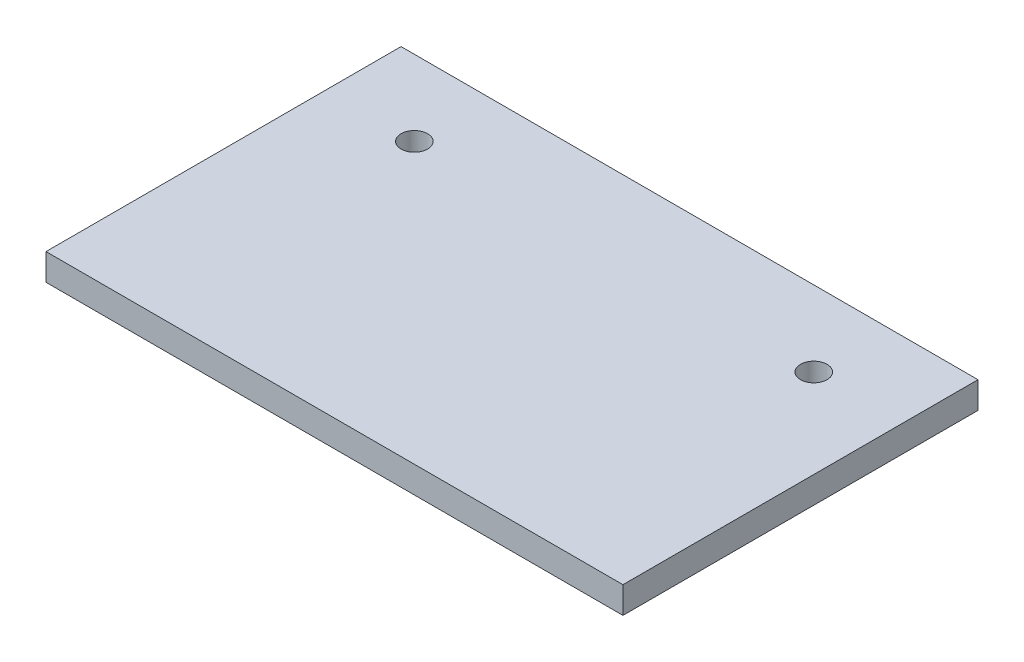
SolidWorks part; units mm, degrees
ref_plane "前视基准面" through (0, 0, 0) normal (0, 0, 1) x (1, 0, 0)
ref_plane "上视基准面" through (0, 0, 0) normal (0, 1, 0) x (1, 0, 0)
ref_plane "右视基准面" through (0, 0, 0) normal (1, 0, 0) x (0, 0, -1)
sketch "草图1" plane through (0, 0, 0) normal (0, 1, 0) x (1, 0, 0)
  line L0 (0, 0) -> (65, 0)
  line L5 (65, 0) -> (65, -40)
  line L6 (65, -40) -> (0, -40)
  line L7 (0, -40) -> (0, 0)
extrude "凸台-拉伸1" add sketch "草图1" along normal blind 3
sketch "草图2" plane through (0, 3, 0) normal (0, 1, 0) x (1, 0, 0)
  line L0 (65, 0) -> (0, 0) construction
  line L1 (0, 0) -> (0, -40) construction
  line L2 (65, -40) -> (65, 0) construction
  circle A0 centre (10, -8.5) radius 1.5
  circle A1 centre (55, -8.5) radius 1.5
  dimension "D1" = 8.5
  dimension "D4" = 10
  dimension "D2" = 8.5
  dimension "D3" = 10
extrude "切除-拉伸1" cut sketch "草图2" against normal blind 3
